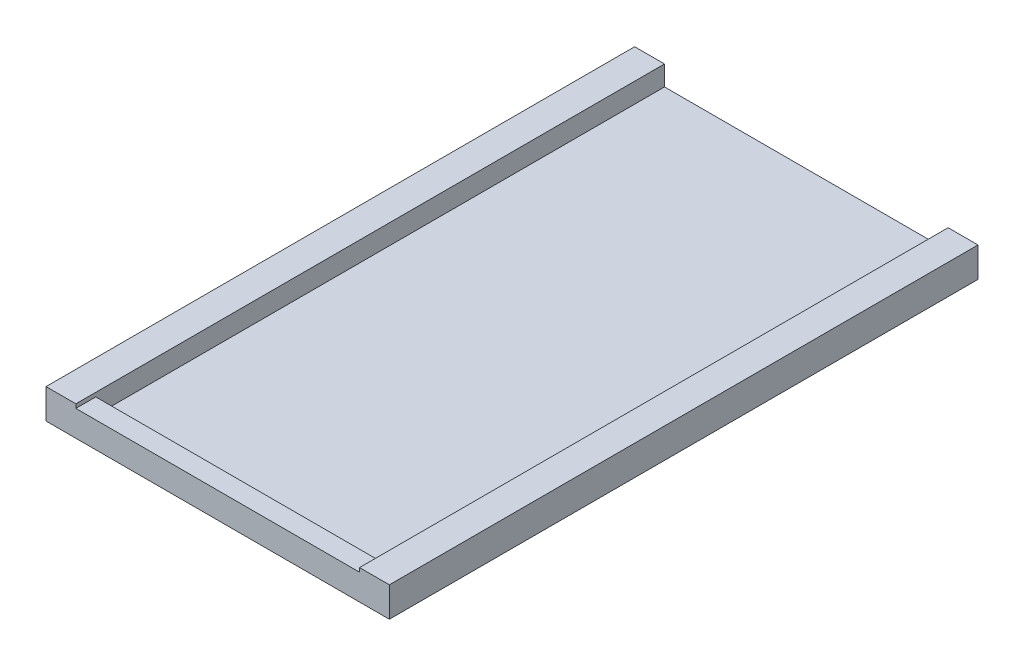
SolidWorks part; units mm, degrees
ref_plane "Front Plane" through (0, 0, 0) normal (0, 0, 1) x (1, 0, 0)
ref_plane "Top Plane" through (0, 0, 0) normal (0, 1, 0) x (1, 0, 0)
ref_plane "Right Plane" through (0, 0, 0) normal (1, 0, 0) x (0, 0, -1)
sketch "Sketch1" plane through (0, 0, 0) normal (0, 1, 0) x (1, 0, 0)
  line L0 (0, 0) -> (17.25, 0)
  line L1 (17.25, 0) -> (17.25, 59.15)
  line L2 (17.25, 59.15) -> (14.25, 59.15)
  line L3 (14.25, 59.15) -> (14.25, 2)
  line L4 (14.25, 2) -> (0, 2)
  line L5 (0, 2) -> (0, 0)
  dimension "D1" = 3
  dimension "D2" = 2
  dimension "D3" = 59.15
  dimension "D4" = 17.25
extrude "Boss-Extrude1" add sketch "Sketch1" along normal blind 2.6
sketch "Sketch3" plane through (0, 2.6, 0) normal (0, 1, 0) x (1, 0, 0)
  line L1 (14.25, 59.15) -> (17.25, 59.15)
  line L2 (14.25, 59.15) -> (14.25, 0)
  line L3 (14.25, 0) -> (17.25, 0)
  line L4 (17.25, 59.15) -> (17.25, 0)
extrude "Boss-Extrude2" add sketch "Sketch3" along normal blind 0.4
mirror "Mirror2" about plane through (0, 0, 0) normal (1, 0, 0) of "Boss-Extrude1", "Boss-Extrude2"
sketch "Sketch5" plane through (0, 0, -2) normal (0, 0, -1) x (-1, 0, 0)
  line L1 (-14.25, 0) -> (14.25, 0)
  line L2 (-14.25, 0) -> (-14.25, 1)
  line L3 (-14.25, 1) -> (14.25, 1)
  line L4 (14.25, 0) -> (14.25, 1)
  dimension "D1" = 1
extrude "Boss-Extrude3" add sketch "Sketch5" along normal through all
